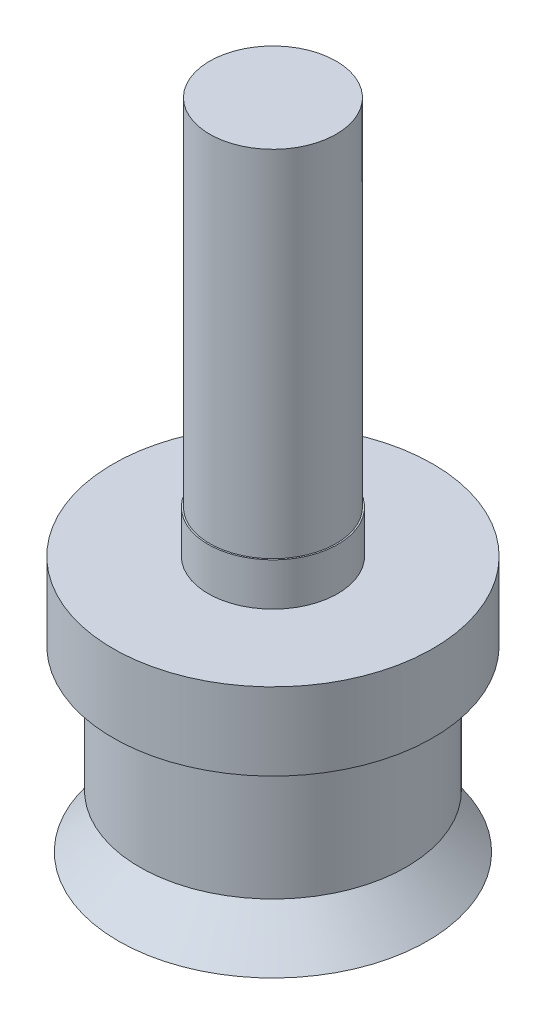
SolidWorks part; units mm, degrees
ref_plane "Alzado" through (0, 0, 0) normal (0, 0, 1) x (1, 0, 0)
ref_plane "Planta" through (0, 0, 0) normal (0, 1, 0) x (1, 0, 0)
ref_plane "Vista lateral" through (0, 0, 0) normal (1, 0, 0) x (0, 0, -1)
sketch "Croquis1" plane through (0, 0, 0) normal (0, 0, 1) x (1, 0, 0)
  line L0 (0, -18.119) -> (0, 13.784) construction
  line L1 (0, 14.9) -> (-2.375, 14.9)
  line L2 (-2.375, 14.9) -> (-2.375, 1.6)
  line L3 (-2.375, 1.6) -> (-2.43, 1.6)
  line L4 (-2.43, 1.6) -> (-2.43, 0)
  line L5 (-2.43, 0) -> (-6, 0)
  line L6 (-6, 0) -> (-6, -2.9)
  line L7 (-6, -2.9) -> (-5, -2.9)
  line L8 (-5, -2.9) -> (-5, -7.6)
  line L9 (-5, -7.6) -> (-3.5, -7.6)
  line L10 (-3.5, -7.6) -> (-5.8, -9.6)
  line L11 (-5.8, -9.6) -> (-1.5, -9.6)
  line L12 (-1.5, -9.6) -> (-1.5, 2.4)
  line L13 (-1.5, 2.4) -> (0, 2.4)
  line L14 (0, 2.4) -> (0, 14.9)
  line L15 (-10.1996, 0) -> (10.44, 0) construction
  point P19 (-6, -9.6)
  point P20 (-3.1787, -7.6)
  dimension "D1" = 24.5
  dimension "D2" = 2.43
  dimension "D3" = 2.375
  dimension "D4" = 1.6
  dimension "D5" = 6
  dimension "D6" = 5
  dimension "D7" = 7.6
  dimension "D8" = 1.5
  dimension "D9" = 12
  dimension "D10" = 4.3
  dimension "D11" = 2
  dimension "D12" = 2.9
  dimension "D13" = 3.5
revolve "Revolución1" add sketch "Croquis1" angle 360 about L0
